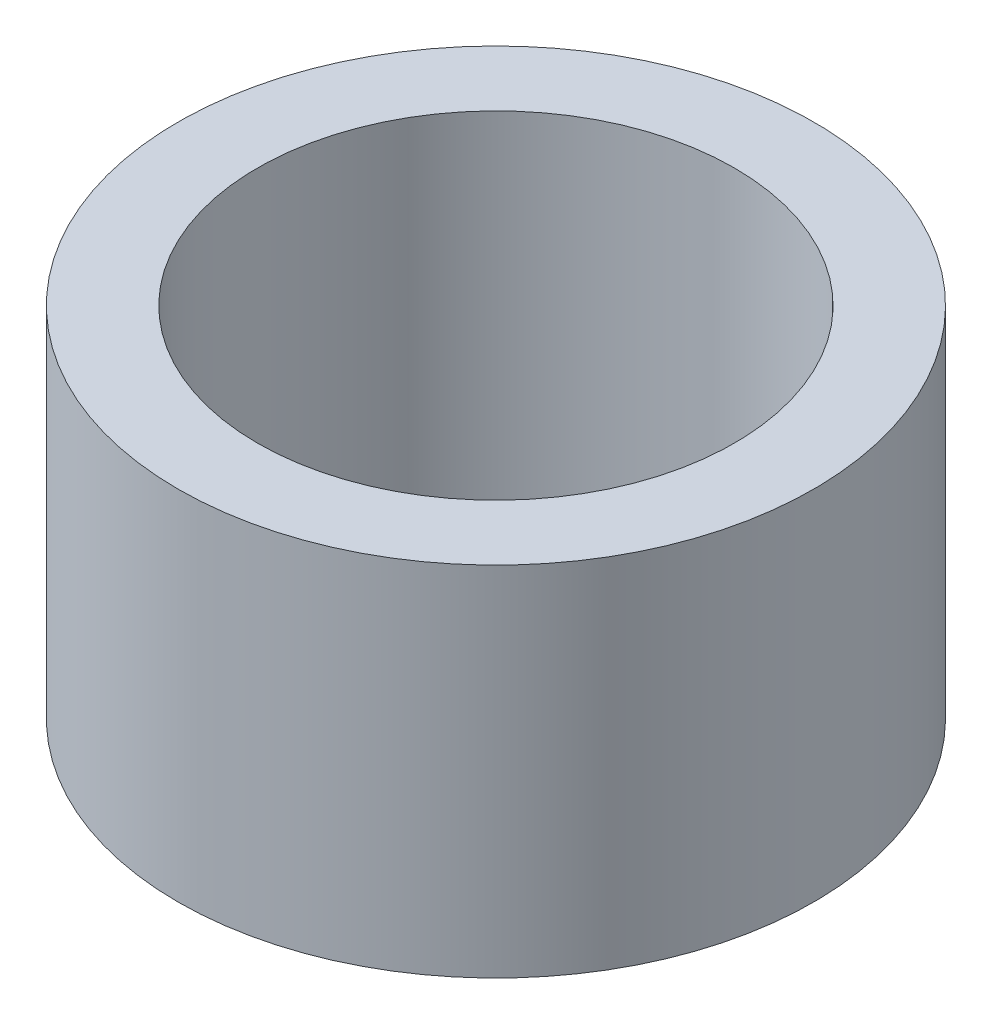
SolidWorks part; units mm, degrees
ref_plane "Front Plane" through (0, 0, 0) normal (0, 0, 1) x (1, 0, 0)
ref_plane "Top Plane" through (0, 0, 0) normal (0, 1, 0) x (1, 0, 0)
ref_plane "Right Plane" through (0, 0, 0) normal (1, 0, 0) x (0, 0, -1)
sketch "Sketch1" plane through (0, 0, 0) normal (0, 1, 0) x (1, 0, 0)
  circle A0 centre (0, 0) radius 3
  circle A1 centre (0, 0) radius 4
  dimension "D1" = 6
  dimension "D2" = 8
extrude "Boss-Extrude2" add sketch "Sketch1" along normal blind 4.5
